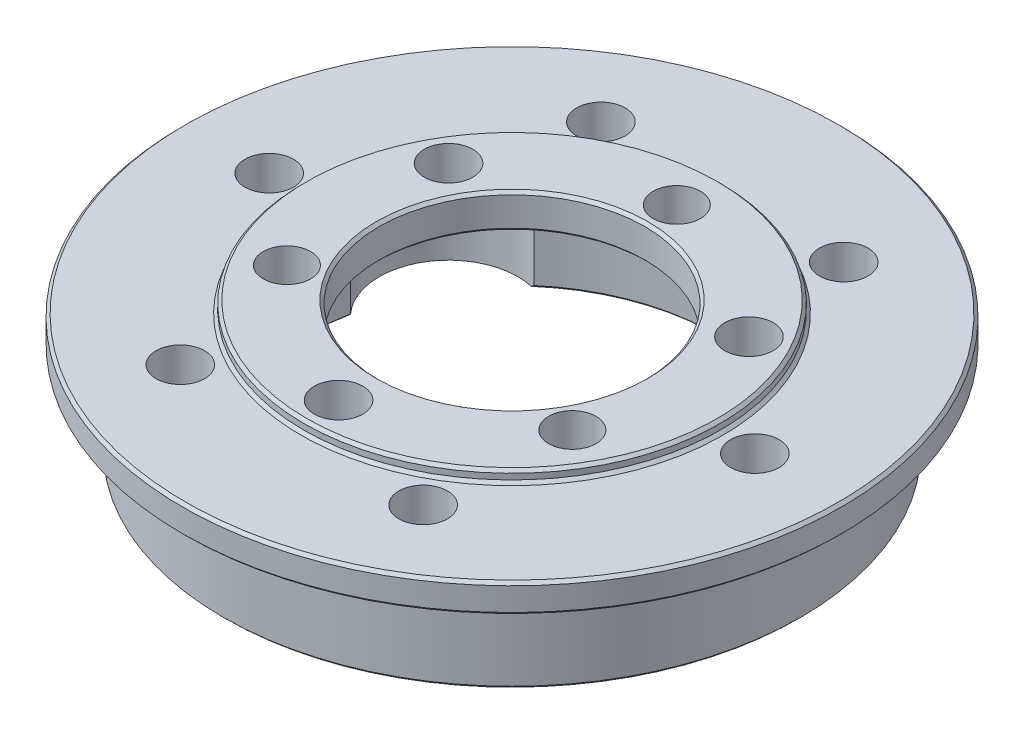
SolidWorks part; units mm, degrees
ref_plane "前视基准面" through (0, 0, 0) normal (0, 0, 1) x (1, 0, 0)
ref_plane "上视基准面" through (0, 0, 0) normal (0, 1, 0) x (1, 0, 0)
ref_plane "右视基准面" through (0, 0, 0) normal (1, 0, 0) x (0, 0, -1)
sketch "草图1" plane through (0, 0, 0) normal (0, 0, 1) x (1, 0, 0)
  line L0 (0, 0) -> (0, 12.6387) construction
  line L1 (-25, 0) -> (-17.5, 0)
  line L2 (-17.5, 0) -> (-17.5, 8.5)
  line L3 (-17.5, 8.5) -> (-11.5, 8.5)
  line L4 (-11.5, 8.5) -> (-11.5, 11.5)
  line L5 (-11.5, 11.5) -> (-18, 11.5)
  line L6 (-18, 11.5) -> (-18, 10.5)
  line L7 (-18, 10.5) -> (-28.5, 10.5)
  line L8 (-28.5, 10.5) -> (-28.5, 8)
  line L9 (-28.5, 8) -> (-25, 8)
  line L10 (-25, 8) -> (-25, 0)
  dimension "D1" = 50
  dimension "D2" = 57
  dimension "D3" = 8
  dimension "D4" = 2.5
  dimension "D5" = 3.5
  dimension "D6" = 23
  dimension "D7" = 35
  dimension "D8" = 3
  dimension "D9" = 36
revolve "旋转1" add sketch "草图1" angle 360 about L0
chamfer "倒角1" distance 0.25 angle 45 10 edges at (0, 8, -28.5) (0, 8, -25) (0, 0, -25) (0, 0, -17.5) (0, 8.5, -17.5) (0, 8.5, -11.5) (0, 11.5, -11.5) (0, 11.5, -18) (0, 10.5, -18) (0, 10.5, -28.5)
sketch "草图2" plane through (0, 8.5, 0) normal (0, -1, 0) x (1, 0, 0)
  circle A0 centre (0, 0) radius 15 construction
  circle A1 centre (0, 0) radius 14.25 construction
  circle A2 centre (0, 15) radius 2.1
  circle A3 centre (0, -14.25) radius 2.05
  point P18 (0, 0)
  dimension "D1" = 28.5
  dimension "D2" = 30
  dimension "D3" = 4.2
  dimension "D4" = 4.1
extrude "切除-拉伸1" cut sketch "草图2" against normal through all
sketch "草图3" plane through (0, 8.5, 0) normal (0, -1, 0) x (1, 0, 0)
  circle A0 centre (0, 15) radius 6
  dimension "D1" = 12
extrude "切除-拉伸2" cut sketch "草图3" along normal through all contours A0
pattern_circular "阵列(圆周)1" count 3 over 360 about axis through (0, 0, 0) along (0, 1, 0) of "切除-拉伸1", "切除-拉伸2"
sketch "草图4" plane through (0, 0, 0) normal (0, -1, 0) x (1, 0, 0)
  line L0 (0, 0) -> (10.5, 18.1865) construction
  line L1 (0, 21) -> (0, 0) construction
  circle A0 centre (0, 0) radius 21 construction
  circle A1 centre (10.5, 18.1865) radius 2.1
  dimension "D1" = 42
  dimension "D3" = 4.2
  dimension "D2" = 30
extrude "切除-拉伸3" cut sketch "草图4" against normal through all
cosmetic thread "装饰螺纹线1" parameters "D2"=5
pattern_circular "阵列(圆周)2" count 6 over 360 about axis through (0, 0, 0) along (0, 1, 0) of "切除-拉伸3"
cosmetic thread "装饰螺纹线2" parameters "D2"=5
cosmetic thread "装饰螺纹线3" parameters "D2"=5
cosmetic thread "装饰螺纹线4" parameters "D2"=5
cosmetic thread "装饰螺纹线5" parameters "D2"=5
cosmetic thread "装饰螺纹线6" parameters "D2"=5
move or copy body "实体-移动/复制1" [suppressed]
